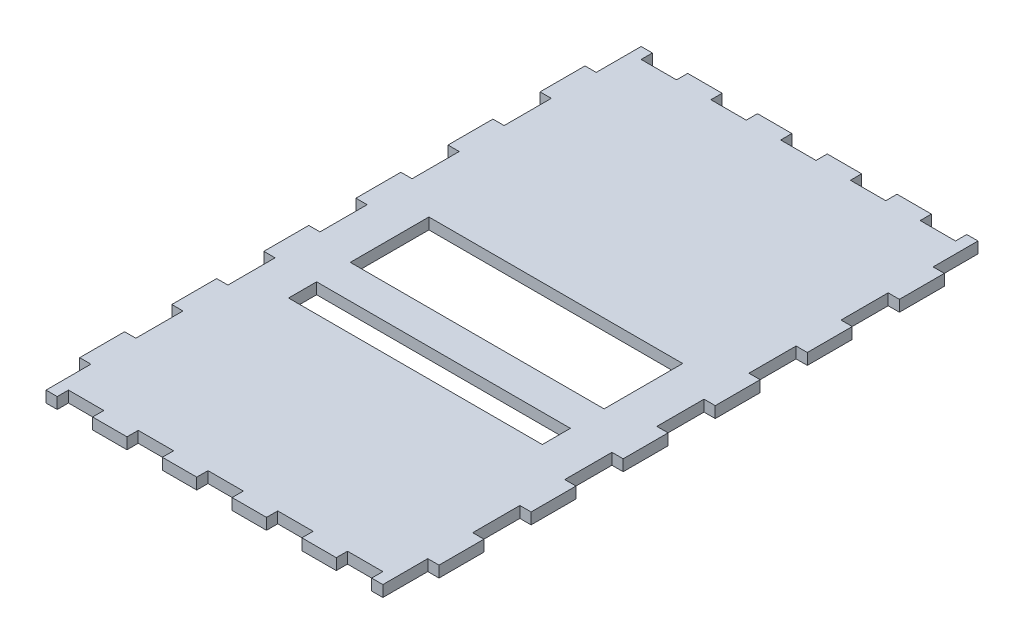
SolidWorks part; units mm, degrees
ref_plane "Front Plane" through (0, 0, 0) normal (0, 0, 1) x (1, 0, 0)
ref_plane "Top Plane" through (0, 0, 0) normal (0, 1, 0) x (1, 0, 0)
ref_plane "Right Plane" through (0, 0, 0) normal (1, 0, 0) x (0, 0, -1)
sketch "Sketch1" plane through (0, 0, 0) normal (0, 1, 0) x (1, 0, 0)
  line L0 (-80, 51.5) -> (-80, 30.5)
  line L1 (-80, 132.5) -> (80, 132.5)
  line L2 (-80, 132.5) -> (-80, -132.5)
  line L3 (-80, -132.5) -> (80, -132.5)
  line L4 (80, 132.5) -> (80, -132.5)
  line L5 (-80, 132.5) -> (80, -132.5) construction
  line L6 (-80, -132.5) -> (80, 132.5) construction
  line L7 (-80, 92.5) -> (-75, 92.5)
  line L8 (-80, 92.5) -> (-80, 71.5)
  line L9 (-80, 71.5) -> (-75, 71.5)
  line L10 (-75, 92.5) -> (-75, 71.5)
  line L11 (-80, 51.5) -> (-75, 51.5)
  line L12 (-75, 51.5) -> (-75, 30.5)
  line L13 (-80, 30.5) -> (-75, 30.5)
  line L14 (-80, 10.5) -> (-80, -10.5)
  line L15 (-80, 10.5) -> (-75, 10.5)
  line L16 (-75, 10.5) -> (-75, -10.5)
  line L17 (-80, -10.5) -> (-75, -10.5)
  line L18 (-80, -30.5) -> (-80, -51.5)
  line L19 (-80, -30.5) -> (-75, -30.5)
  line L20 (-75, -30.5) -> (-75, -51.5)
  line L21 (-80, -51.5) -> (-75, -51.5)
  line L22 (-80, -71.5) -> (-80, -92.5)
  line L23 (-80, -71.5) -> (-75, -71.5)
  line L24 (-75, -71.5) -> (-75, -92.5)
  line L25 (-80, -92.5) -> (-75, -92.5)
  line L26 (0, 132.5) -> (0, -132.5) construction
  line L27 (-80, 132.5) -> (-75, 132.5)
  line L28 (-80, 132.5) -> (-80, 112.5)
  line L29 (-80, 112.5) -> (-75, 112.5)
  line L30 (-75, 132.5) -> (-75, 112.5)
  line L31 (-80, -132.5) -> (-75, -132.5)
  line L32 (-80, -132.5) -> (-80, -112.5)
  line L33 (-80, -112.5) -> (-75, -112.5)
  line L34 (-75, -132.5) -> (-75, -112.5)
  line L35 (80, -112.5) -> (75, -112.5)
  line L36 (75, -132.5) -> (75, -112.5)
  line L37 (80, -132.5) -> (75, -132.5)
  line L38 (80, -132.5) -> (80, -112.5)
  line L39 (80, -71.5) -> (75, -71.5)
  line L40 (75, -71.5) -> (75, -92.5)
  line L41 (80, -92.5) -> (75, -92.5)
  line L42 (80, -71.5) -> (80, -92.5)
  line L43 (80, -30.5) -> (75, -30.5)
  line L44 (75, -30.5) -> (75, -51.5)
  line L45 (80, -51.5) -> (75, -51.5)
  line L46 (80, -30.5) -> (80, -51.5)
  line L47 (80, 10.5) -> (75, 10.5)
  line L48 (75, 10.5) -> (75, -10.5)
  line L49 (80, -10.5) -> (75, -10.5)
  line L50 (80, 10.5) -> (80, -10.5)
  line L51 (80, 51.5) -> (75, 51.5)
  line L52 (75, 51.5) -> (75, 30.5)
  line L53 (80, 30.5) -> (75, 30.5)
  line L54 (80, 51.5) -> (80, 30.5)
  line L55 (80, 71.5) -> (75, 71.5)
  line L56 (75, 92.5) -> (75, 71.5)
  line L57 (80, 92.5) -> (75, 92.5)
  line L58 (80, 92.5) -> (80, 71.5)
  line L59 (80, 112.5) -> (75, 112.5)
  line L60 (75, 132.5) -> (75, 112.5)
  line L61 (80, 132.5) -> (75, 132.5)
  line L62 (80, 132.5) -> (80, 112.5)
  line L63 (-38.9375, 132.5) -> (-38.9375, 127.5)
  line L64 (-70, 132.5) -> (-54.25, 132.5)
  line L65 (-70, 132.5) -> (-70, 127.5)
  line L66 (-70, 127.5) -> (-54.25, 127.5)
  line L67 (-54.25, 132.5) -> (-54.25, 127.5)
  line L68 (-38.9375, 132.5) -> (-23.1875, 132.5)
  line L69 (-23.1875, 132.5) -> (-23.1875, 127.5)
  line L70 (-38.9375, 127.5) -> (-23.1875, 127.5)
  line L71 (-7.875, 132.5) -> (-7.875, 127.5)
  line L72 (-7.875, 132.5) -> (7.875, 132.5)
  line L73 (7.875, 132.5) -> (7.875, 127.5)
  line L74 (-7.875, 127.5) -> (7.875, 127.5)
  line L75 (23.1875, 132.5) -> (23.1875, 127.5)
  line L76 (23.1875, 132.5) -> (38.9375, 132.5)
  line L77 (38.9375, 132.5) -> (38.9375, 127.5)
  line L78 (23.1875, 127.5) -> (38.9375, 127.5)
  line L79 (54.25, 132.5) -> (54.25, 127.5)
  line L80 (54.25, 132.5) -> (70, 132.5)
  line L81 (70, 132.5) -> (70, 127.5)
  line L82 (54.25, 127.5) -> (70, 127.5)
  line L83 (-80, 0) -> (80, 0) construction
  line L84 (-7.875, -132.5) -> (7.875, -132.5)
  line L85 (7.875, -132.5) -> (7.875, -127.5)
  line L86 (-7.875, -127.5) -> (7.875, -127.5)
  line L87 (-7.875, -132.5) -> (-7.875, -127.5)
  line L88 (54.25, -132.5) -> (70, -132.5)
  line L89 (70, -132.5) -> (70, -127.5)
  line L90 (54.25, -127.5) -> (70, -127.5)
  line L91 (54.25, -132.5) -> (54.25, -127.5)
  line L92 (23.1875, -132.5) -> (38.9375, -132.5)
  line L93 (38.9375, -132.5) -> (38.9375, -127.5)
  line L94 (23.1875, -127.5) -> (38.9375, -127.5)
  line L95 (23.1875, -132.5) -> (23.1875, -127.5)
  line L96 (-38.9375, -132.5) -> (-23.1875, -132.5)
  line L97 (-23.1875, -132.5) -> (-23.1875, -127.5)
  line L98 (-38.9375, -127.5) -> (-23.1875, -127.5)
  line L99 (-38.9375, -132.5) -> (-38.9375, -127.5)
  line L100 (-70, -127.5) -> (-54.25, -127.5)
  line L101 (-54.25, -132.5) -> (-54.25, -127.5)
  line L102 (-70, -132.5) -> (-54.25, -132.5)
  line L103 (-70, -132.5) -> (-70, -127.5)
  point P0 (0, 0)
  dimension "D1" = 160
  dimension "D2" = 265
  dimension "D3" = 21
  dimension "D4" = 40
  dimension "D5" = 5
  dimension "D7" = 40
  dimension "D8" = 5
  dimension "D9" = 20
  dimension "D10" = 10
  dimension "D11" = 15.75
  dimension "D12" = 5
  dimension "D14" = 10
  dimension "D6" = 5
  dimension "D13" = 5
extrude "Boss-Extrude1" add sketch "Sketch1" along normal blind 5 contours L3 L103 L100 L101 L99 L98 L97 L87 L86 L85 L95 L94 L93 L91 L90 L89 L36 L35 L4 L41 L40 L39 L45 L44 L43 L49 L48 L47 L53 L52 L51 L55 L56 L57 L59 L60 L1 L81 L82 L79
sketch "Sketch2" plane through (0, 5, 0) normal (0, 1, 0) x (1, 0, 0)
  line L0 (-70, 127.5) -> (-54.25, 127.5) construction
  line L1 (-56.5, 19.5) -> (56.5, 19.5)
  line L2 (-56.5, 19.5) -> (-56.5, -15.5)
  line L3 (-56.5, -15.5) -> (56.5, -15.5)
  line L4 (56.5, 19.5) -> (56.5, -15.5)
  line L6 (-56.5, -30.5) -> (56.5, -30.5)
  line L7 (-56.5, -30.5) -> (-56.5, -43)
  line L8 (-56.5, -43) -> (56.5, -43)
  line L9 (56.5, -30.5) -> (56.5, -43)
  point P6 (0, 19.5)
  dimension "D1" = 108
  dimension "D2" = 35
  dimension "D3" = 113
  dimension "D4" = 15
  dimension "D5" = 12.5
extrude "Cut-Extrude1" cut sketch "Sketch2" against normal blind 10
